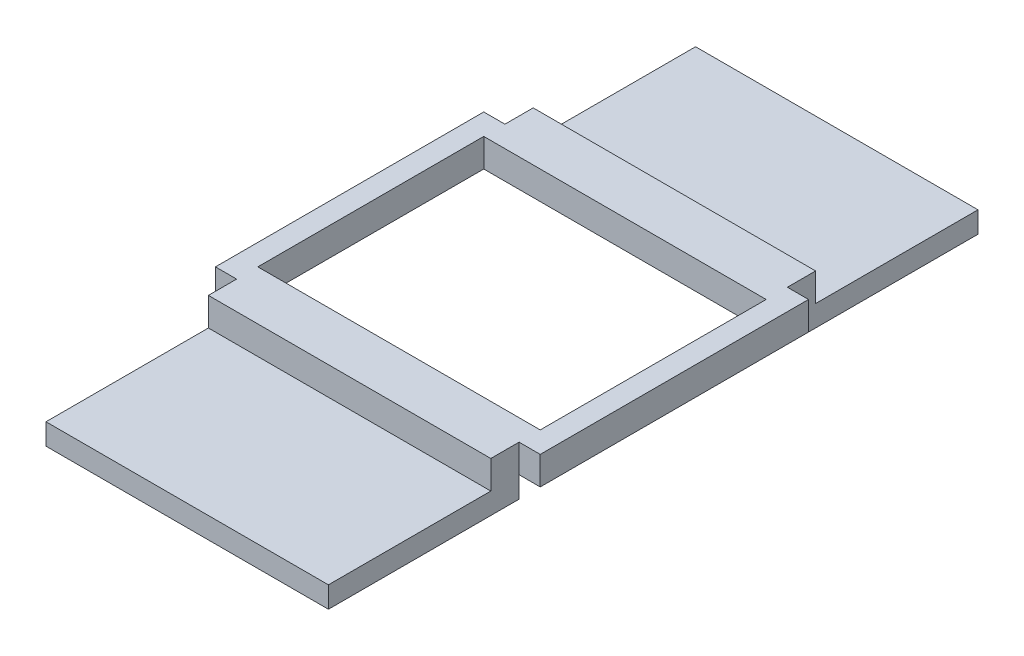
SolidWorks part; units mm, degrees
ref_plane "Front Plane" through (0, 0, 0) normal (0, 0, 1) x (1, 0, 0)
ref_plane "Top Plane" through (0, 0, 0) normal (0, 1, 0) x (1, 0, 0)
ref_plane "Right Plane" through (0, 0, 0) normal (1, 0, 0) x (0, 0, -1)
sketch "Sketch1" plane through (0, 0, 0) normal (0, 1, 0) x (1, 0, 0)
  line L1 (-10, 8) -> (10, 8)
  line L2 (-10, 8) -> (-10, -8)
  line L3 (-10, -8) -> (10, -8)
  line L4 (10, 8) -> (10, -8)
  line L5 (-10, 8) -> (10, -8) construction
  line L6 (-10, -8) -> (10, 8) construction
  line L7 (-11.5, 9.5) -> (11.5, 9.5)
  line L8 (-11.5, 9.5) -> (-11.5, -9.5)
  line L9 (-11.5, -9.5) -> (11.5, -9.5)
  line L10 (11.5, 9.5) -> (11.5, -9.5)
  line L11 (-11.5, 9.5) -> (11.5, -9.5) construction
  line L12 (-11.5, -9.5) -> (11.5, 9.5) construction
  point P0 (0, 0)
  point P6 (0, 0)
  dimension "D1" = 20
  dimension "D2" = 16
  dimension "D3" = 23
  dimension "D4" = 19
extrude "Boss-Extrude1" add sketch "Sketch1" along normal blind 2
sketch "Sketch2" plane through (0, 0, 0) normal (0, -1, 0) x (1, 0, 0)
  line L0 (0, 0) -> (0, -17.9077) construction
  line L9 (0, 0) -> (8.2059, 0) construction
  line L10 (10, -8) -> (10, -23)
  line L11 (-10, 8) -> (10, 8)
  line L12 (-10, 8) -> (-10, 23)
  line L13 (-10, 23) -> (10, 23)
  line L14 (10, 8) -> (10, 23)
  line L15 (-10, -23) -> (10, -23)
  line L16 (-10, -8) -> (-10, -23)
  line L17 (-10, -8) -> (10, -8)
  line L18 (-11.5, 9.5) -> (11.5, 9.5) construction
  line L19 (-10, 8) -> (10, 8)
  line L20 (-10, 8) -> (-10, 9.5)
  line L21 (-10, 9.5) -> (10, 9.5)
  line L22 (10, 8) -> (10, 9.5)
  line L23 (11.5, -9.5) -> (-11.5, -9.5) construction
  line L24 (-10, -8) -> (10, -8)
  line L25 (-10, -8) -> (-10, -9.5)
  line L26 (-10, -9.5) -> (10, -9.5)
  line L27 (10, -8) -> (10, -9.5)
  line M2 (11.5, 9.5) -> (-11.5, 9.5)
  line M4 (-11.5, -9.5) -> (11.5, -9.5)
  dimension "D1" = 20
  dimension "D2" = 15
extrude "Boss-Extrude3" add sketch "Sketch2" along normal blind 1.5 separate body contours L14 L13 L12 M2 | L16 L15 L10 M4
sketch "Sketch3" plane through (0, 0, 0) normal (0, 1, 0) x (1, 0, 0)
  line L0 (-10, 9.5) -> (-10, 23) construction
  line L1 (10, 9.5) -> (-10, 9.5)
  line L2 (10, 9.5) -> (10, 11.5)
  line L3 (10, 11.5) -> (-10, 11.5)
  line L4 (-10, 9.5) -> (-10, 11.5)
  line L5 (10, -9.5) -> (10, -23) construction
  line L6 (-10, -9.5) -> (10, -9.5)
  line L7 (-10, -9.5) -> (-10, -11.5)
  line L8 (-10, -11.5) -> (10, -11.5)
  line L9 (10, -9.5) -> (10, -11.5)
  dimension "D1" = 2
  dimension "D2" = 2
extrude "Boss-Extrude4" add sketch "Sketch3" along normal blind 2
